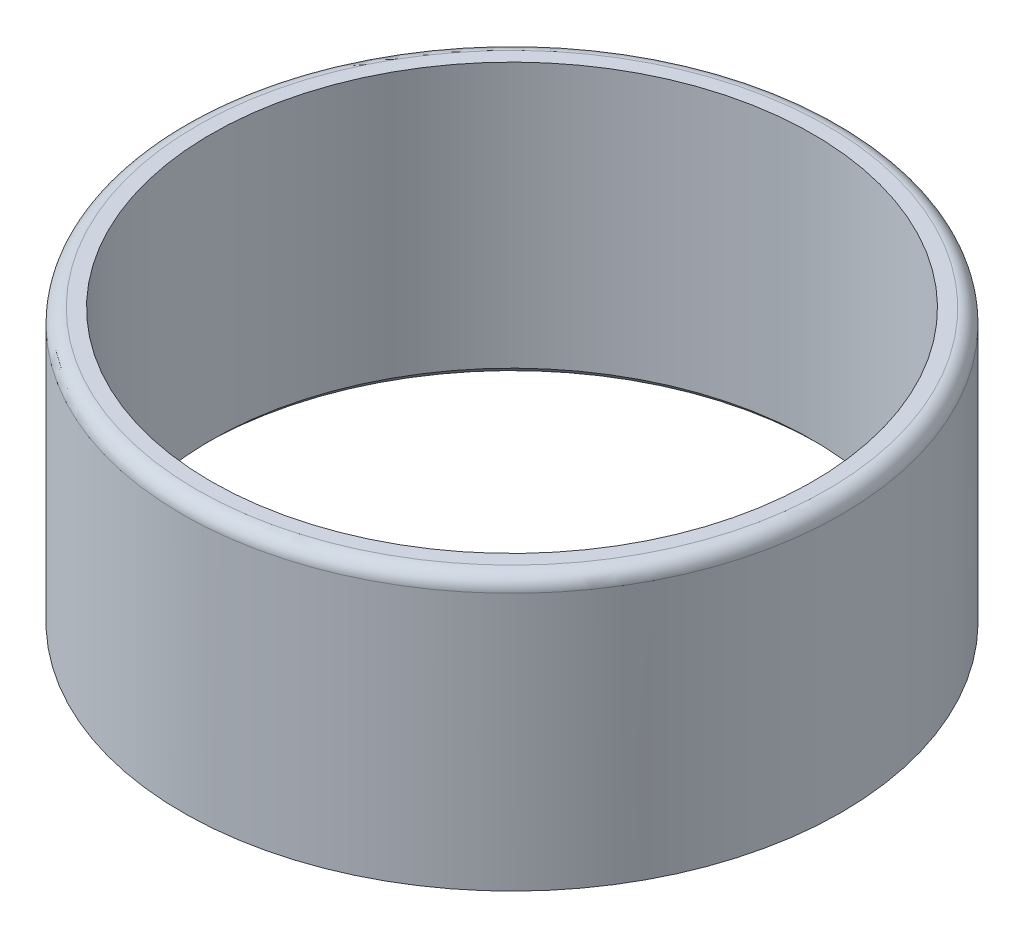
SolidWorks part; units mm, degrees
ref_plane "Front Plane" through (0, 0, 0) normal (0, 0, 1) x (1, 0, 0)
ref_plane "Top Plane" through (0, 0, 0) normal (0, 1, 0) x (1, 0, 0)
ref_plane "Right Plane" through (0, 0, 0) normal (1, 0, 0) x (0, 0, -1)
sketch "Sketch1" plane through (0, 0, 0) normal (0, 1, 0) x (1, 0, 0)
  circle A0 centre (0, 0) radius 21
extrude "Extrude-Thin1" add sketch "Sketch1" along normal blind 19 thin
fillet "Fillet1" radius 1 1 edges at (23, 19, 0)
chamfer "Chamfer1" distance 0.5 angle 45 1 edges at (0, 0, 21)
